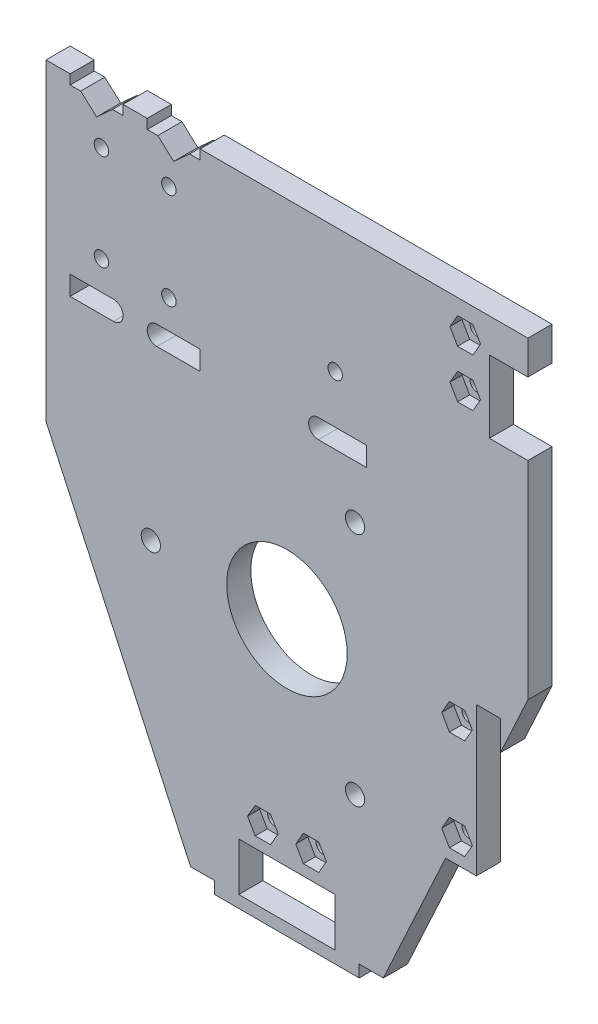
SolidWorks part; units mm, degrees
material "1060 合金"
ref_plane "前视基准面" through (0, 0, 0) normal (0, 0, 1) x (1, 0, 0)
ref_plane "上视基准面" through (0, 0, 0) normal (0, 1, 0) x (1, 0, 0)
ref_plane "右视基准面" through (0, 0, 0) normal (1, 0, 0) x (0, 0, -1)
sketch "草图1" plane through (0, 0, 0) normal (0, 0, 1) x (1, 0, 0)
  line L1 (0, 0) -> (100, 0)
  line L2 (0, 0) -> (0, 130)
  line L3 (0, 130) -> (100, 130)
  line L4 (100, 0) -> (100, 130)
  dimension "D1" = 100
  dimension "D2" = 130
extrude "凸台-拉伸1" add sketch "草图1" along normal blind 8
sketch "草图2" plane through (0, 0, 8) normal (0, 0, 1) x (1, 0, 0)
  line L0 (0, 130) -> (0, 0) construction
  line L1 (0, 0) -> (100, 0) construction
  circle A0 centre (50, 54.5) radius 25
  dimension "D1" = 50
  dimension "D2" = 50
  dimension "D3" = 54.5
sketch "草图3" plane through (0, 0, 8) normal (0, 0, 1) x (1, 0, 0)
  line L0 (0, 0) -> (100, 0) construction
  line L1 (40, 0) -> (60, 0)
  line L2 (40, 0) -> (40, 10)
  line L3 (40, 10) -> (60, 10)
  line L4 (60, 0) -> (60, 10)
  line L5 (0, 130) -> (0, 0) construction
  line L6 (0, 0) -> (30, 0)
  line L7 (30, 0) -> (0, 65)
  line L8 (0, 65) -> (0, 0)
  line L9 (100, 0) -> (100, 65)
  line L10 (100, 0) -> (100, 130) construction
  line L11 (100, 65) -> (70, 0)
  line L12 (70, 0) -> (100, 0)
  dimension "D1" = 20
  dimension "D2" = 10
  dimension "D3" = 40
  dimension "D4" = 30
  dimension "D5" = 30
extrude "切除-拉伸1" cut sketch "草图3" against normal blind 8
sketch "草图4" plane through (0, 0, 0) normal (0, 0, -1) x (-1, 0, 0)
  line L0 (-56.5, 94) -> (-66.5, 94)
  line L1 (-100, 65) -> (-100, 130) construction
  line L2 (-100, 108) -> (-92, 108)
  line L3 (-100, 108) -> (-100, 123)
  line L4 (-100, 123) -> (-92, 123)
  line L5 (-66.5, 94) -> (-66.5, 90)
  line L6 (-66.5, 90) -> (-56.5, 90)
  line L7 (-32, 94) -> (-32, 90)
  line L8 (-32, 90) -> (-23, 90)
  line L9 (-23, 94) -> (-32, 94)
  line L10 (-5, 94) -> (-5, 90)
  line L11 (-5, 90) -> (-14, 90)
  line L12 (-14, 94) -> (-5, 94)
  line L13 (-10.5, 125) -> (-13.8, 128)
  line L14 (-100, 130) -> (0, 130) construction
  line L15 (-13.8, 128) -> (-10.5, 125) construction
  line L16 (-16, 130) -> (-5, 130)
  line L17 (-10.5, 125) -> (-7.2, 128) construction
  line L18 (-7.2, 128) -> (-10.5, 125)
  line L19 (-26.5, 125) -> (-29.8, 128)
  line L20 (-29.8, 128) -> (-26.5, 125) construction
  line L21 (-32, 130) -> (-21, 130)
  line L22 (-26.5, 125) -> (-23.2, 128) construction
  line L23 (-23.2, 128) -> (-26.5, 125)
  line L24 (-21, 130) -> (-21, 128)
  line L25 (-92, 108) -> (-92, 123)
  line L26 (-100, 108) -> (-80, 108) construction
  line L27 (-21, 128) -> (-23.2, 128)
  line L28 (-32, 128) -> (-32, 130)
  line L29 (-29.8, 128) -> (-32, 128)
  line L30 (-5, 130) -> (-5, 128)
  line L31 (-5, 128) -> (-7.2, 128)
  line L32 (-60, 10) -> (-40, 10) construction
  line L33 (-13.8, 128) -> (-16, 128)
  line L34 (-16, 128) -> (-16, 130)
  line L35 (-40, 10) -> (-40, 0) construction
  line L36 (-60, 0) -> (-60, 10) construction
  arc A0 (-56.5, 90) -> (-56.5, 94) centre (-56.5, 92) ccw
  arc A1 (-23, 90) -> (-23, 94) centre (-23, 92) ccw
  arc A2 (-14, 90) -> (-14, 94) centre (-14, 92) cw
  circle A4 centre (-87, 124) radius 1.5
  circle A5 centre (-25.5, 100) radius 1.5
  circle A6 centre (-11.5, 100) radius 1.5
  circle A7 centre (-11.5, 120) radius 1.5
  circle A8 centre (-25.5, 120) radius 1.5
  circle A9 centre (-60, 104) radius 1.5
  circle A10 centre (-45, 15) radius 1.5
  circle A11 centre (-55, 15) radius 1.5
  circle A15 centre (-87, 114) radius 1.5
  dimension "D1" = 5
  dimension "D2" = 5
  dimension "D3" = 5
  dimension "D4" = 5
extrude "切除-拉伸2" cut sketch "草图4" against normal through all
sketch "草图9" plane through (0, 0, 8) normal (0, 0, 1) x (1, 0, 0)
  line L1 (90.1754, 124) -> (88.5877, 126.75)
  line L2 (88.5877, 126.75) -> (85.4123, 126.75)
  line L3 (85.4123, 126.75) -> (83.8246, 124)
  line L4 (83.8246, 124) -> (85.4123, 121.25)
  line L5 (85.4123, 121.25) -> (88.5877, 121.25)
  line L6 (88.5877, 121.25) -> (90.1754, 124)
  line L7 (90.1754, 114) -> (88.5877, 116.75)
  line L8 (88.5877, 116.75) -> (85.4123, 116.75)
  line L9 (85.4123, 116.75) -> (83.8246, 114)
  line L10 (83.8246, 114) -> (85.4123, 111.25)
  line L11 (85.4123, 111.25) -> (88.5877, 111.25)
  line L12 (88.5877, 111.25) -> (90.1754, 114)
  line L13 (48.1754, 15) -> (46.5877, 17.75)
  line L14 (46.5877, 17.75) -> (43.4123, 17.75)
  line L15 (43.4123, 17.75) -> (41.8246, 15)
  line L16 (41.8246, 15) -> (43.4123, 12.25)
  line L17 (43.4123, 12.25) -> (46.5877, 12.25)
  line L18 (46.5877, 12.25) -> (48.1754, 15)
  line L19 (58.1754, 15) -> (56.5877, 17.75)
  line L20 (56.5877, 17.75) -> (53.4123, 17.75)
  line L21 (53.4123, 17.75) -> (51.8246, 15)
  line L22 (51.8246, 15) -> (53.4123, 12.25)
  line L23 (53.4123, 12.25) -> (56.5877, 12.25)
  line L24 (56.5877, 12.25) -> (58.1754, 15)
  circle A0 centre (45, 15) radius 2.75 construction
  circle A1 centre (55, 15) radius 2.75 construction
  circle A2 centre (87, 124) radius 2.75 construction
  circle A3 centre (87, 114) radius 2.75 construction
  dimension "D1" = 5.5
  dimension "D2" = 5.5
  dimension "D3" = 5.5
  dimension "D4" = 5.5
extrude "切除-拉伸6" cut sketch "草图9" against normal blind 2.5
sketch "草图10" plane through (0, 0, 8) normal (0, 0, 1) x (1, 0, 0)
  line L0 (94.3, 58.8) -> (89.3, 58.8)
  line L1 (89.3, 58.8) -> (89.3, 28)
  line L2 (89.3, 28) -> (94.3, 28)
  line L3 (94.3, 28) -> (94.3, 58.8)
  circle A0 centre (50, 54.5) radius 12.5
  dimension "D1" = 25
extrude "切除-拉伸7" cut sketch "草图10" against normal through all
sketch "草图12" plane through (0, 0, 8) normal (0, 0, 1) x (1, 0, 0)
  line L0 (89.3, 41.8167) -> (82.9231, 28)
  line L1 (89.3, 41.8167) -> (70, 0) construction
  line L2 (81.3, 28) -> (94.3, 28) construction
  line L3 (82.9231, 28) -> (89.3, 28)
  line L4 (89.3, 28) -> (89.3, 41.8167)
extrude "凸台-拉伸3" add sketch "草图12" against normal blind 8
sketch "草图5" plane through (0, 0, 8) normal (0, 0, 1) x (1, 0, 0)
  circle A0 centre (21.75, 54.5) radius 2
  circle A1 centre (64.125, 78.9652) radius 2
  circle A2 centre (64.125, 30.0348) radius 2
  circle A3 centre (50, 54.5) radius 12.5 construction
  circle A4 centre (85.3, 53.8) radius 1.5
  circle A5 centre (85.3, 33) radius 1.5
  dimension "D2" = 4
  dimension "D1" = 28.25
  dimension "D3" = 0
  dimension "D4" = 3
extrude "切除-拉伸3" cut sketch "草图5" against normal through all
sketch "草图11" plane through (0, 0, 8) normal (0, 0, 1) x (1, 0, 0)
  line L0 (30, 0) -> (40, 0) construction
  line L1 (35, 0) -> (65, 0)
  line L2 (35, 0) -> (35, -2.5)
  line L3 (35, -2.5) -> (65, -2.5)
  line L4 (65, 0) -> (65, -2.5)
  dimension "D1" = 2.5
extrude "凸台-拉伸2" add sketch "草图11" against normal blind 8
sketch "草图14" plane through (0, 0, 8) normal (0, 0, 1) x (1, 0, 0)
  line L1 (88.4754, 53.8) -> (86.8877, 56.55)
  line L2 (86.8877, 56.55) -> (83.7123, 56.55)
  line L3 (83.7123, 56.55) -> (82.1246, 53.8)
  line L4 (82.1246, 53.8) -> (83.7123, 51.05)
  line L5 (83.7123, 51.05) -> (86.8877, 51.05)
  line L6 (86.8877, 51.05) -> (88.4754, 53.8)
  line L7 (88.4754, 33) -> (86.8877, 35.75)
  line L8 (86.8877, 35.75) -> (83.7123, 35.75)
  line L9 (83.7123, 35.75) -> (82.1246, 33)
  line L10 (82.1246, 33) -> (83.7123, 30.25)
  line L11 (83.7123, 30.25) -> (86.8877, 30.25)
  line L12 (86.8877, 30.25) -> (88.4754, 33)
  circle A0 centre (85.3, 53.8) radius 2.75 construction
  circle A1 centre (85.3, 33) radius 2.75 construction
  dimension "D1" = 5.5
  dimension "D2" = 5.5
extrude "切除-拉伸8" cut sketch "草图14" against normal blind 2.5
sketch "草图15" plane through (0, 0, 0) normal (0, 0, -1) x (-1, 0, 0)
  line L1 (0, 130) -> (-100, 130)
  line L2 (0, 130) -> (0, -5)
  line L3 (0, -5) -> (-100, -5)
  line L4 (-100, 130) -> (-100, -5)
  dimension "D1" = 100
  dimension "D2" = 135
extrude "切除-拉伸9" cut sketch "草图15" against normal blind 3
